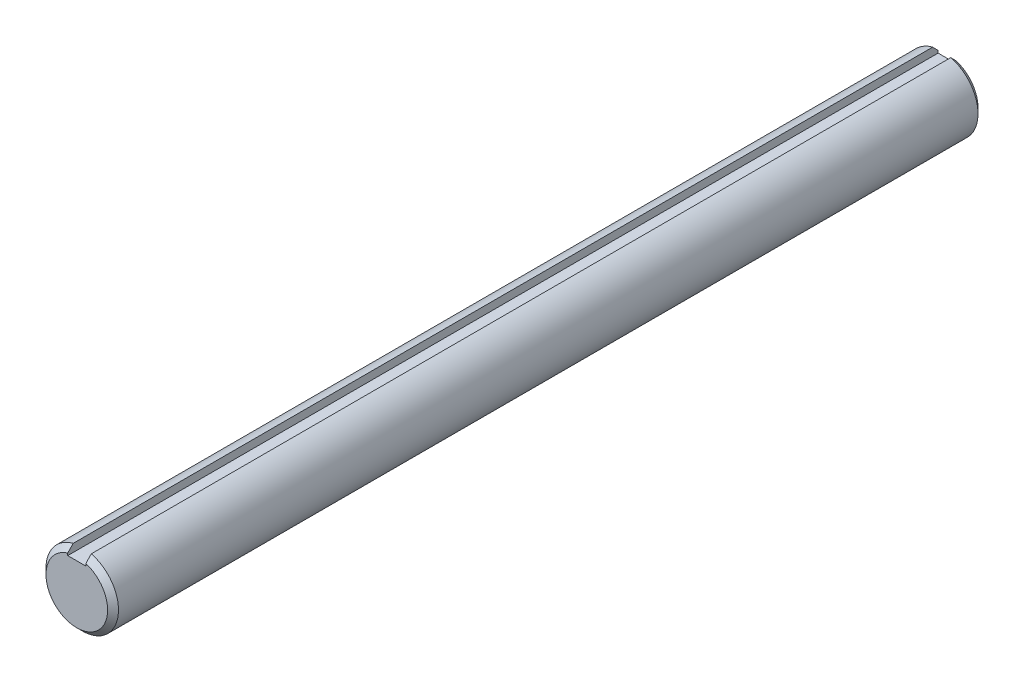
SolidWorks part; units mm, degrees
ref_plane "Front" through (0, 0, 0) normal (0, 0, 1) x (1, 0, 0)
ref_plane "Top" through (0, 0, 0) normal (0, 1, 0) x (1, 0, 0)
ref_plane "Right" through (0, 0, 0) normal (1, 0, 0) x (0, 0, -1)
sketch "Sketch1" plane through (0, 0, 0) normal (0, 0, 1) x (1, 0, 0)
  circle A0 centre (0, 0) radius 6.35
  dimension "dia" = 12.7
extrude "Extrude1" add sketch "Sketch1" along normal mid plane 152.4
sketch "Sketch2" plane through (0, 0, 0) normal (1, 0, 0) x (0, 0, -1)
  point P0 (-76.2, 6.35)
  point P1 (76.2, 6.35)
  point P2 (76.2, -6.35)
chamfer "Chamfer1" distance 0.9525 angle 45 2 edges at (6.35, 0, -76.2) (6.35, 0, 76.2)
sketch "Sketch3" plane through (0, 0, 0) normal (0, 0, 1) x (1, 0, 0)
  line L1 (-1.5875, 6.35) -> (1.5875, 6.35)
  line L2 (-1.5875, 6.35) -> (-1.5875, 4.7625)
  line L3 (-1.5875, 4.7625) -> (1.5875, 4.7625)
  line L4 (1.5875, 6.35) -> (1.5875, 4.7625)
  dimension "key wd" = 3.175
  dimension "key dp" = 1.5875
extrude "Extrude2" cut sketch "Sketch3" against normal through all and the other way through all
equation "\"D1@Chamfer1\" = \"dia@Sketch1\" * .075"
